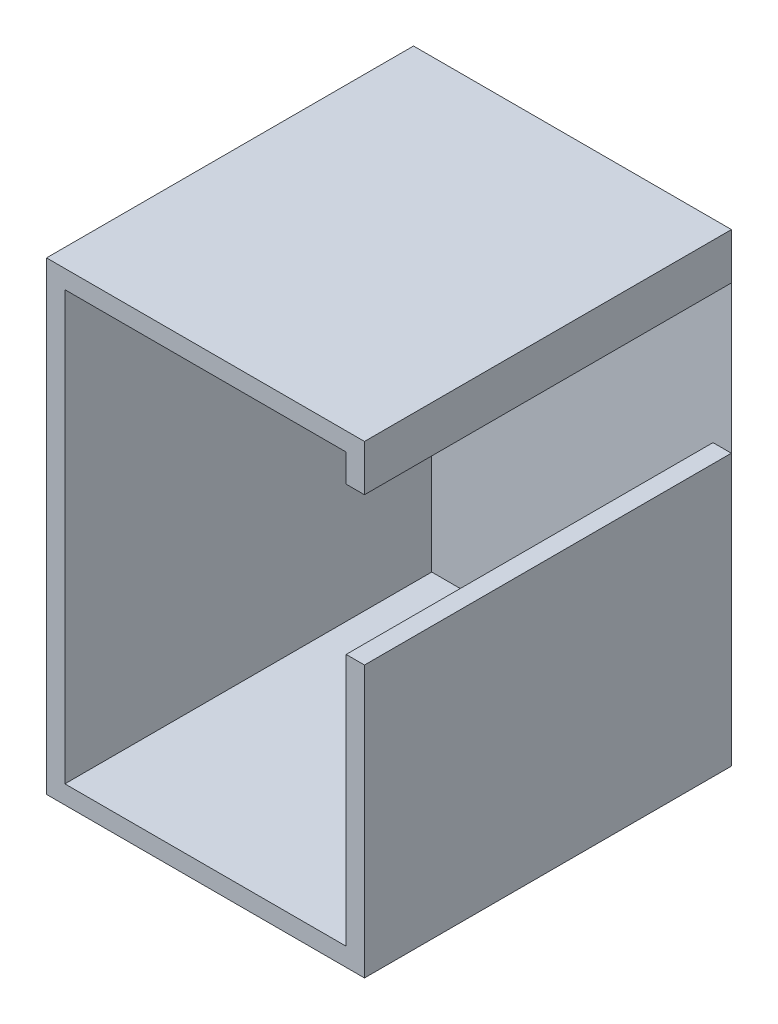
SolidWorks part; units mm, degrees
ref_plane "Front Plane" through (0, 0, 0) normal (0, 0, 1) x (1, 0, 0)
ref_plane "Top Plane" through (0, 0, 0) normal (0, 1, 0) x (1, 0, 0)
ref_plane "Right Plane" through (0, 0, 0) normal (1, 0, 0) x (0, 0, -1)
sketch "Sketch1" plane through (0, 0, 0) normal (0, 0, 1) x (1, 0, 0)
  line L0 (0, -227.6148) -> (150, -227.6148)
  line L1 (0, 0) -> (-2300, 0)
  line L2 (0, -1433.3365) -> (0, -3500)
  line L3 (0, -3500) -> (-2300, -3500)
  line L4 (-2300, 0) -> (-2300, -3500)
  line L5 (150, 150) -> (-2450, 150)
  line L6 (150, -1433.3365) -> (150, -3650)
  line L7 (150, -3650) -> (-2450, -3650)
  line L8 (-2450, 150) -> (-2450, -3650)
  line L9 (0, 0) -> (0, -227.6148)
  line L10 (150, -1433.3365) -> (0, -1433.3365)
  line L11 (150, 150) -> (150, -227.6148)
  dimension "D1" = 2300
  dimension "D2" = 3500
  dimension "D3" = 150
  dimension "D4" = 150
  dimension "D5" = 150
  dimension "D6" = 150
extrude "Boss-Extrude1" add sketch "Sketch1" along normal blind 3000
sketch "Sketch2" plane through (0, 0, 0) normal (0, 0, -1) x (-1, 0, 0)
  line L1 (2450, -3650) -> (-150, -3650)
  line L2 (2450, -3650) -> (2450, 150)
  line L3 (2450, 150) -> (-150, 150)
  line L4 (-150, -3650) -> (-150, 150)
extrude "Boss-Extrude2" add sketch "Sketch2" along normal blind 1
